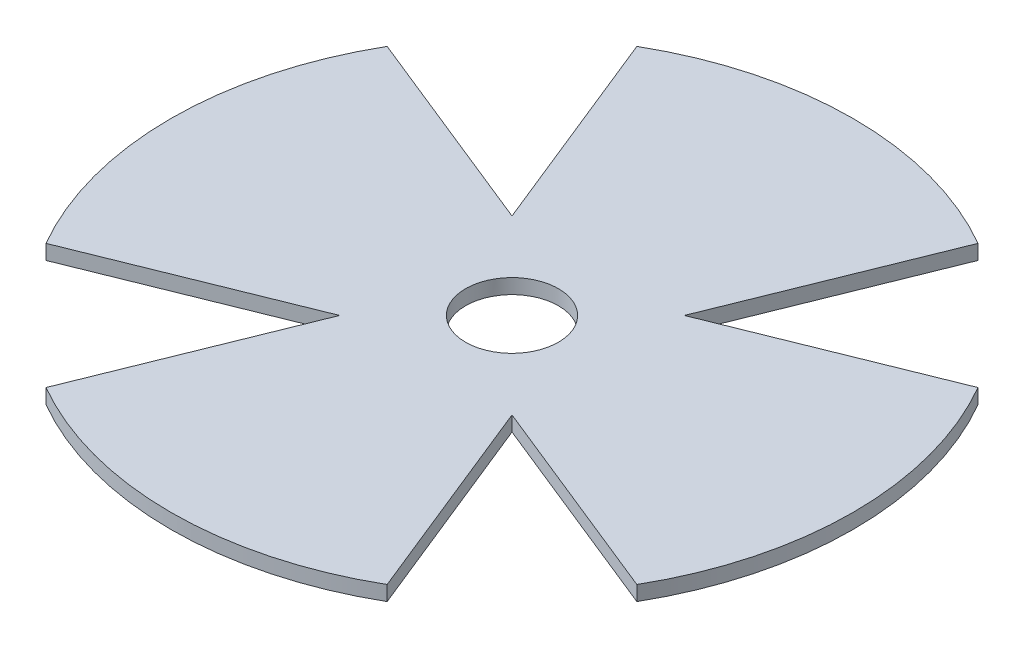
SolidWorks part; units mm, degrees
material "1023 Carbon Steel Sheet (SS)"
ref_plane "Front Plane" through (0, 0, 0) normal (0, 0, 1) x (1, 0, 0)
ref_plane "Top Plane" through (0, 0, 0) normal (0, 1, 0) x (1, 0, 0)
ref_plane "Right Plane" through (0, 0, 0) normal (1, 0, 0) x (0, 0, -1)
sketch "Sketch1" plane through (0, 0, 0) normal (0, 1, 0) x (1, 0, 0)
  line L0 (-17.5, 30.3109) -> (-17.5, 17.5)
  line L9 (-17.5, 17.5) -> (-30.3109, 17.5)
  line L10 (-17.5, -30.3109) -> (-17.5, -17.5)
  line L11 (-17.5, -17.5) -> (-30.3109, -17.5)
  line L12 (17.5, -30.3109) -> (17.5, -17.5)
  line L13 (17.5, -17.5) -> (30.3109, -17.5)
  line L14 (17.5, 30.3109) -> (17.5, 17.5)
  line L15 (17.5, 17.5) -> (30.3109, 17.5)
  arc A1 (-17.5, 30.3109) -> (17.5, 30.3109) centre (0, 0) cw
  arc A2 (30.3109, 17.5) -> (30.3109, -17.5) centre (0, 0) cw
  arc A3 (17.5, -30.3109) -> (-17.5, -30.3109) centre (0, 0) cw
  arc A4 (-30.3109, -17.5) -> (-30.3109, 17.5) centre (0, 0) cw
  dimension "D1" = 35
  dimension "D4" = 35
  dimension "D5" = 35
  dimension "D6" = 35
  dimension "D2" = 35
  dimension "D3" = 35
extrude "Boss-Extrude1" add sketch "Sketch1" along normal blind 1.52
sketch "Sketch2" plane through (0, 0, 0) normal (0, 1, 0) x (1, 0, 0)
  line L1 (17.5, 17.5) -> (0, 0)
  line L2 (-30.3109, 17.5) -> (-17.5, 30.3109)
  line L3 (17.5, 30.3109) -> (30.3109, 17.5)
  line L4 (30.3109, -17.5) -> (17.5, -30.3109)
  line L5 (-30.3109, -17.5) -> (-17.5, -30.3109)
  line L9 (17.5, 30.3109) -> (8.8388, 8.8388)
  line L10 (8.8388, 8.8388) -> (30.3109, 17.5)
  line L11 (-17.5, 30.3109) -> (-8.8388, 8.8388)
  line L12 (-8.8388, 8.8388) -> (-30.3109, 17.5)
  line L13 (-30.3109, -17.5) -> (-8.8388, -8.8388)
  line L14 (-8.8388, -8.8388) -> (-17.5, -30.3109)
  line L15 (30.3109, -17.5) -> (8.8388, -8.8388)
  line L16 (8.8388, -8.8388) -> (17.5, -30.3109)
  circle A1 centre (0, 0) radius 4.7625
  circle A2 centre (0, 0) radius 12.5
  point P17 (0, 0)
  dimension "D2" = 9.525
  dimension "D3" = 25
extrude "Cut-Extrude5" cut sketch "Sketch2" against normal through all and the other way through all contours L13 L14 L5 | L16 L4 L15 | L10 L3 L9 | L11 L12 L2 | A1
